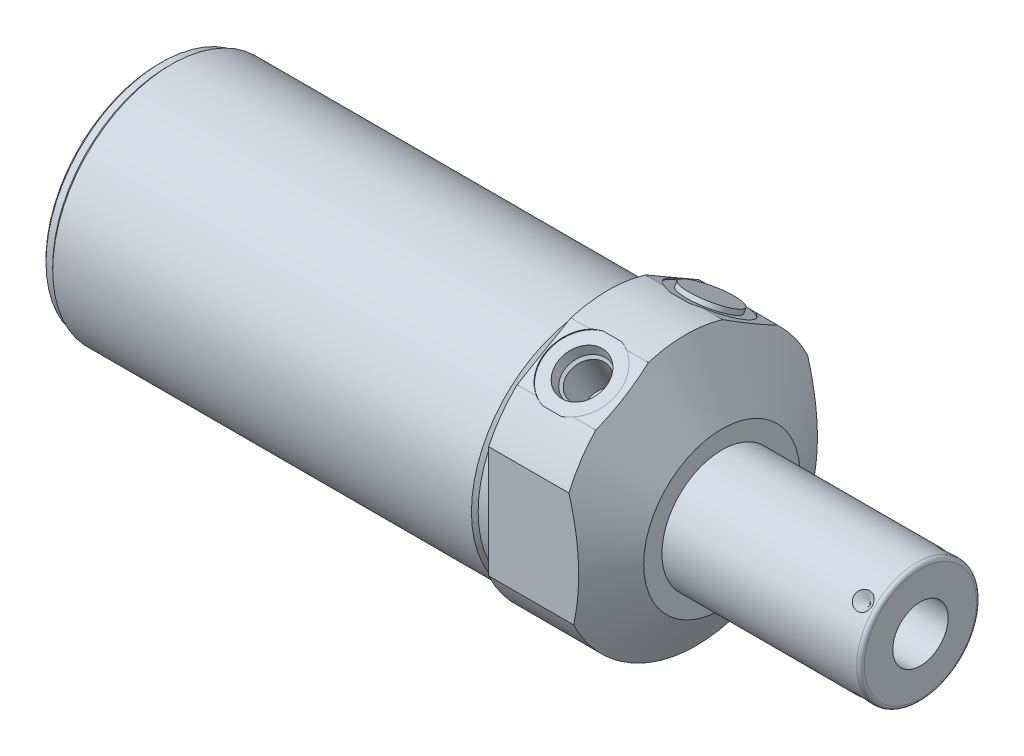
SolidWorks part; units mm, degrees
material "Alloy Steel"
ref_plane "Front Plane" through (0, 0, 0) normal (0, 0, 1) x (1, 0, 0)
ref_plane "Top Plane" through (0, 0, 0) normal (0, 1, 0) x (1, 0, 0)
ref_plane "Right Plane" through (0, 0, 0) normal (1, 0, 0) x (0, 0, -1)
ref_plane "Plane1" through (0, 0, 0) normal (1, 0, 0) x (0, 0, -1)
sketch "Sketch1" plane through (0, 0, 0) normal (1, 0, 0) x (0, 0, -1)
  circle A0 centre (0, 0) radius 34.925
  dimension "D1" = 69.85
extrude "Extrude1" add sketch "Sketch1" along normal blind 30.1498 and the other way blind 119.0752
ref_plane "Plane2" through (0, 0, 0) normal (1, 0, 0) x (0, 0, -1)
sketch "Sketch2" plane through (0, 0, 0) normal (1, 0, 0) x (0, 0, -1)
  line L0 (-34.6456, -2.54) -> (34.6456, -2.54) construction
  circle A0 centre (0, -2.54) radius 31.496
  circle A1 centre (0, 0) radius 34.925 construction
  circle A2 centre (0, 0) radius 34.925
  dimension "D1" = 62.992
  dimension "D2" = 2.54
extrude "Cut-Extrude1" cut sketch "Sketch2" against normal up to next
ref_plane "Plane4" through (0, 0, 0) normal (-1, 0, 0) x (0, 0, 1)
sketch "Sketch4" plane through (0, 0, 0) normal (-1, 0, 0) x (0, 0, 1)
  line L0 (31.623, -14.8237) -> (31.623, 20.9382)
  line L1 (31.623, 20.9382) -> (0, 39.1957)
  line L2 (-31.623, -14.8237) -> (-31.623, 20.9382)
  line L3 (-31.623, 20.9382) -> (0, 39.1957)
  line L4 (0, -38.631) -> (0, 42.9018) construction
  circle A0 centre (0, 0) radius 34.925 construction
  arc A1 (-31.623, -14.8237) -> (31.623, -14.8237) centre (0, 0) ccw
  circle A2 centre (0, 0) radius 41.275
  dimension "D4" = 82.55
  dimension "D1" = 63.246
  dimension "D2" = 120
  dimension "D3" = 36.1442
extrude "Cut-Extrude3" cut sketch "Sketch4" against normal up to next
ref_plane "Plane6" through (0, 0, 0) normal (0, 0, 1) x (1, 0, 0)
sketch "Sketch6" plane through (0, 0, 0) normal (0, 0, 1) x (1, 0, 0)
  line L0 (0.3071, 69.85) -> (30.1498, 18.161)
  line L1 (-1.185, -2.54) -> (31.6419, -2.54) construction
  line L2 (-119.0752, -2.54) -> (0, -2.54) construction
  line L3 (30.1498, 25.2881) -> (30.1498, 33.5055) construction
  line L4 (30.1498, 18.161) -> (30.1498, 69.85)
  line L5 (30.1498, 69.85) -> (0.3071, 69.85)
  line L6 (30.1498, -14.8237) -> (30.1498, 14.8237) construction
  dimension "D1" = 41.402
  dimension "D2" = 30
  dimension "D3" = 144.78
revolve "Cut-Revolve2" cut sketch "Sketch6" angle 360 about L1
ref_plane "Plane7" through (9.9568, 29.1768, 16.8452) normal (1, 0, 0) x (0, 0.5, -0.866)
sketch "S2D0002" plane through (9.9568, 29.1768, 16.8452) normal (1, 0, 0) x (0, 0.5, -0.866)
  line L0 (0, 0) -> (6.1849, 0)
  line L1 (6.1849, 0) -> (5.6423, -2.5527)
  line L2 (5.6423, -2.5527) -> (4.9784, -3.2166)
  line L3 (4.9784, -3.2166) -> (4.9784, -13.462)
  line L4 (4.9784, -13.462) -> (0, -13.462)
  line L5 (0, -13.462) -> (0, 0)
  line L6 (0, -14.1351) -> (0, 0.6731) construction
  dimension "D1" = 13.462
revolve "Cut-Revolve3" cut sketch "S2D0002" angle 360 about L6
ref_plane "Plane8" through (9.9568, 29.1768, -16.8452) normal (1, 0, 0) x (0, -0.5, -0.866)
sketch "Sketch8" plane through (9.9568, 29.1768, -16.8452) normal (1, 0, 0) x (0, -0.5, -0.866)
  line L0 (0, 0) -> (6.1849, 0)
  line L1 (6.1849, 0) -> (5.6423, -2.5527)
  line L2 (5.6423, -2.5527) -> (4.9784, -3.2166)
  line L3 (4.9784, -3.2166) -> (4.9784, -13.462)
  line L4 (4.9784, -13.462) -> (0, -13.462)
  line L5 (0, -13.462) -> (0, 0)
  line L6 (0, -14.1351) -> (0, 0.6731) construction
  dimension "D1" = 13.462
revolve "Cut-Revolve4" cut sketch "Sketch8" angle 360 about L6
ref_plane "Plane10" through (0, 0, 0) normal (0, 0, 1) x (1, 0, 0)
sketch "Sketch18" plane through (0, 29.3968, 16.9722) normal (0, 0.866, 0.5) x (1, 0, 0)
  circle A0 centre (9.9568, 0) radius 9.525
  dimension "D1" = 19.05
extrude "Cut-Extrude4" cut sketch "Sketch18" against normal blind 0.254
sketch "Sketch19" plane through (0, 29.3968, -16.9722) normal (0, 0.866, -0.5) x (1, 0, 0)
  circle A0 centre (9.9568, 0) radius 9.525
  dimension "D1" = 19.05
extrude "Cut-Extrude5" cut sketch "Sketch19" against normal blind 0.254
sketch "Sketch10" plane through (0, 0, 0) normal (0, 0, 1) x (1, 0, 0)
  line L0 (0, 28.956) -> (0, 28.067)
  line L1 (0, 28.067) -> (-3.81, 28.067)
  line L2 (-3.81, 28.067) -> (-4.699, 28.956)
  line L3 (-4.9339, -2.54) -> (0.2349, -2.54) construction
  line L4 (0, 28.956) -> (-4.699, 28.956)
  line L5 (-119.0752, -2.54) -> (0, -2.54) construction
  line L6 (0, 28.956) -> (-119.0752, 28.956) construction
  line L7 (0, 25.2881) -> (0, 33.5055) construction
  dimension "D1" = 3.81
  dimension "D2" = 45
  dimension "D3" = 61.214
revolve "Cut-Revolve6" cut sketch "Sketch10" angle 360 about L3
ref_plane "Plane12" through (0, 0, 0) normal (0, 0, 1) x (1, 0, 0)
sketch "Sketch12" plane through (0, 0, 0) normal (0, 0, 1) x (1, 0, 0)
  line L0 (-119.0752, 28.956) -> (-119.0752, 28.067)
  line L1 (-119.0752, 28.067) -> (-116.5352, 28.067)
  line L2 (-116.5352, 28.067) -> (-115.6462, 28.956)
  line L3 (-119.2466, -2.54) -> (-115.4748, -2.54) construction
  line L4 (-119.0752, 28.956) -> (-115.6462, 28.956)
  line L5 (-119.0752, -2.54) -> (-4.699, -2.54) construction
  line L6 (-4.699, 28.956) -> (-119.0752, 28.956) construction
  line L7 (-119.0752, 28.956) -> (-119.0752, -34.036) construction
  dimension "D1" = 61.214
  dimension "D2" = 2.54
  dimension "D3" = 45
revolve "Cut-Revolve8" cut sketch "Sketch12" angle 360 about L3
chamfer "Chamfer1" distance 0.762 angle 45 1 edges at (-119.0752, -2.54, 30.607)
ref_plane "Plane13" through (0, 0, 0) normal (0, 0, 1) x (0, -1, 0)
sketch "Sketch13" plane through (0, 0, 0) normal (0, 0, 1) x (0, -1, 0)
  line L0 (2.54, 30.1498) -> (2.54, 82.7786)
  line L1 (2.54, 82.7786) -> (17.399, 82.7786)
  line L2 (18.415, 81.7626) -> (18.415, 30.1498)
  line L3 (18.415, 30.1498) -> (2.54, 30.1498)
  line L4 (2.54, 27.5184) -> (2.54, 85.41) construction
  line L5 (2.54, -115.6462) -> (2.54, -4.699) construction
  line L6 (23.241, 30.1498) -> (-18.161, 30.1498) construction
  line L7 (-28.067, 0) -> (33.147, 0) construction
  arc A0 (18.415, 81.7626) -> (17.399, 82.7786) centre (17.399, 81.7626) ccw
  dimension "D3" = 1.016
  dimension "D1" = 31.75
  dimension "D2" = 82.7786
revolve "Revolve1" add sketch "Sketch13" angle 360 about L4
ref_plane "Plane14" through (82.7786, -9.8806, 0) normal (0, 0, 1) x (0, -1, 0)
sketch "S2D0001" plane through (82.7786, -9.8806, 0) normal (0, 0, 1) x (0, -1, 0)
  line L0 (0, 0) -> (0, -25.4)
  line L1 (0, -25.4) -> (-7.3406, -29.8107)
  line L2 (0, 0) -> (-7.3406, 0)
  line L3 (-7.3406, 0) -> (-7.3406, -29.8107)
  line L4 (-7.3406, -31.3012) -> (-7.3406, 1.4905) construction
  line L5 (7.5184, 0) -> (-22.1996, 0) construction
  line L6 (-7.3406, -1.016) -> (-7.3406, -52.6288) construction
  dimension "D1" = 14.6812
  dimension "D2" = 25.4
  dimension "D3" = 59
revolve "Cut-Revolve9" cut sketch "S2D0001" angle 360 about L4
ref_plane "Plane15" through (30.1498, 29.1768, -16.8452) normal (0, -0.866, 0.5) x (0, -0.5, -0.866)
sketch "Sketch15" plane through (30.1498, 29.1768, -16.8452) normal (0, -0.866, 0.5) x (0, -0.5, -0.866)
  circle A0 centre (0, -20.193) radius 6.9469
  arc A1 (9.2036, -17.7395) -> (-9.2036, -17.7395) centre (0, -20.193) ccw construction
  dimension "D1" = 13.8938
extrude "Extrude2" add sketch "Sketch15" against normal blind 1.27
ref_plane "Plane16" through (78.8162, -18.415, 0) normal (0, 0, 1) x (-1, 0, 0)
ref_plane "Plane18" through (0, -1.27, -1.27) normal (0, 0.7071, 0.7071) x (-1, 0, 0)
sketch "Sketch16" plane through (78.8162, 8.6853, -11.2253) normal (0, -0.7071, -0.7071) x (-1, 0, 0)
  line L0 (0, 0) -> (2.413, 0)
  line L1 (2.413, 0) -> (0, -2.413)
  line L2 (0, 0) -> (0, -2.413)
  line L3 (0, -2.5337) -> (0, 0.1207) construction
  line L4 (48.6664, 0) -> (-2.9464, 0) construction
  line L5 (-3.9624, -1.016) -> (-3.9624, -30.734) construction
  dimension "D1" = 3.9624
  dimension "D2" = 4.826
  dimension "D3" = 45
revolve "Cut-Revolve10" cut sketch "Sketch16" angle 360 about L3
ref_plane "Plane17" through (78.8162, 13.335, 0) normal (0, 0, 1) x (1, 0, 0)
pattern_circular "CirPattern1" count 4 over 360 about axis through (27.5184, -2.54, 0) along (-1, 0, 0) of "Cut-Revolve10"
